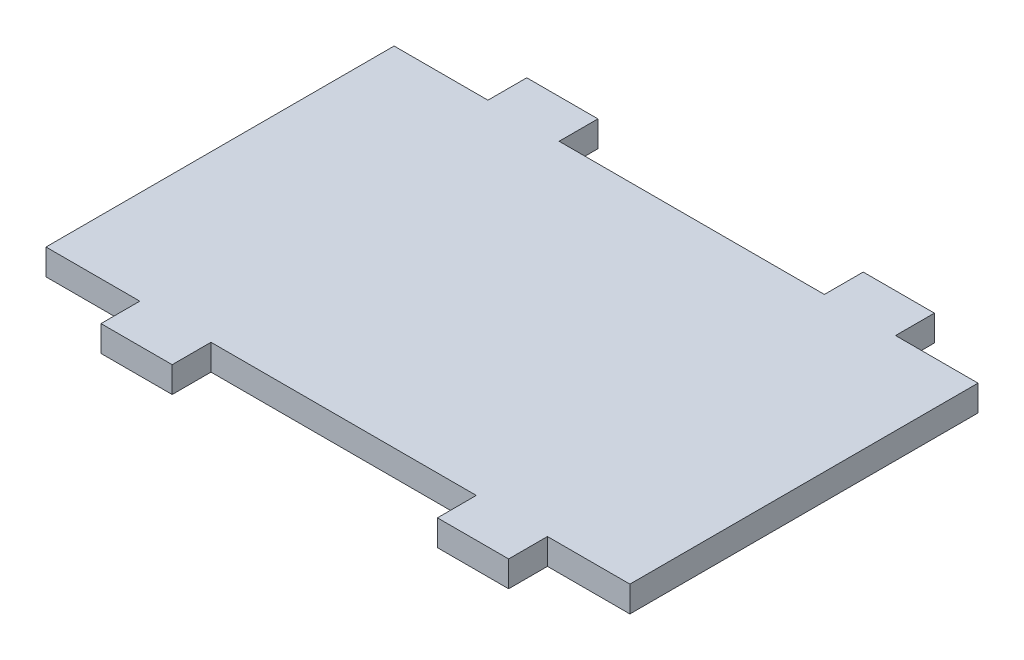
SolidWorks part; units mm, degrees
ref_plane "Front Plane" through (0, 0, 0) normal (0, 0, 1) x (1, 0, 0)
ref_plane "Top Plane" through (0, 0, 0) normal (0, 1, 0) x (1, 0, 0)
ref_plane "Right Plane" through (0, 0, 0) normal (1, 0, 0) x (0, 0, -1)
sketch "Sketch1" plane through (0, 0, 0) normal (0, 1, 0) x (1, 0, 0)
  line L1 (-50.7984, -5.3305) -> (-28.2384, -5.3305)
  line L2 (-50.7984, -5.3305) -> (-50.7984, -18.7805)
  line L3 (-50.7984, -18.7805) -> (-28.2384, -18.7805)
  line L4 (-28.2384, -5.3305) -> (-28.2384, -18.7805)
  dimension "D1" = 13.45
  dimension "D2" = 22.56
sketch "Sketch2" plane through (0, 0, 0) normal (0, 1, 0) x (1, 0, 0)
  line L0 (-50.7984, -5.3305) -> (-28.2384, -5.3305) construction
  line L1 (-47.1734, -5.3305) -> (-44.4234, -5.3305)
  line L2 (-47.1734, -5.3305) -> (-47.1734, -3.8305)
  line L3 (-47.1734, -3.8305) -> (-44.4234, -3.8305)
  line L4 (-44.4234, -5.3305) -> (-44.4234, -3.8305)
  line L5 (-50.7984, -5.3305) -> (-50.7984, -18.7805) construction
  line L6 (-28.2384, -5.3305) -> (-28.2384, -18.7805) construction
  line L7 (-50.7984, -18.7805) -> (-28.2384, -18.7805) construction
  line L8 (-47.1734, -18.7805) -> (-44.4234, -18.7805)
  line L9 (-47.1734, -18.7805) -> (-47.1734, -20.2805)
  line L10 (-47.1734, -20.2805) -> (-44.4234, -20.2805)
  line L11 (-44.4234, -18.7805) -> (-44.4234, -20.2805)
  line L12 (-34.1734, -5.3305) -> (-34.1734, -3.8305)
  line L13 (-34.1734, -3.8305) -> (-31.4234, -3.8305)
  line L14 (-31.4234, -5.3305) -> (-31.4234, -3.8305)
  line L15 (-34.1734, -5.3305) -> (-31.4234, -5.3305)
  line L16 (-34.1734, -18.7805) -> (-31.4234, -18.7805)
  line L17 (-31.4234, -18.7805) -> (-31.4234, -20.2805)
  line L18 (-34.1734, -20.2805) -> (-31.4234, -20.2805)
  line L19 (-34.1734, -18.7805) -> (-34.1734, -20.2805)
  dimension "D1" = 2.75
  dimension "D2" = 3.625
  dimension "D3" = 16.185
  dimension "D4" = 1.5
  dimension "D5" = 1.5
  dimension "D6" = 2.75
  dimension "D7" = 3.625
  dimension "D8" = 2
extrude "Boss-Extrude1" add sketch "Sketch1" along normal blind 1
extrude "Boss-Extrude2" add sketch "Sketch2" along normal blind 1
